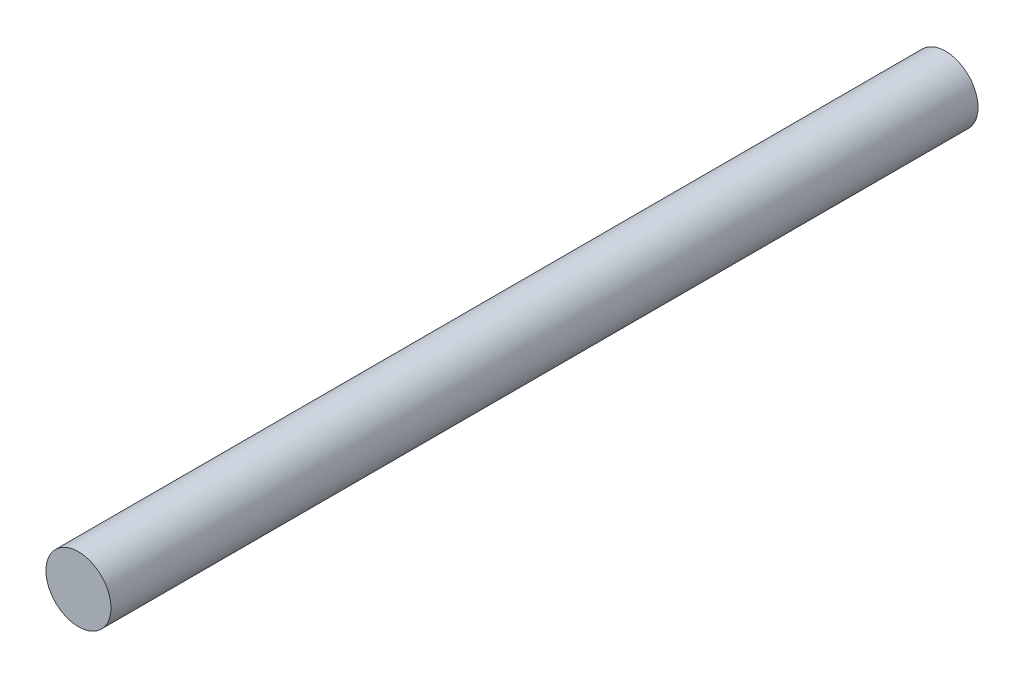
SolidWorks part; units mm, degrees
ref_plane "Front Plane" through (0, 0, 0) normal (0, 0, 1) x (1, 0, 0)
ref_plane "Top Plane" through (0, 0, 0) normal (0, 1, 0) x (1, 0, 0)
ref_plane "Right Plane" through (0, 0, 0) normal (1, 0, 0) x (0, 0, -1)
sketch "Sketch1" plane through (0, 0, 0) normal (0, 0, 1) x (1, 0, 0)
  circle A0 centre (0, 0) radius 0.75
  dimension "D1" = 1.5
extrude "Boss-Extrude1" add sketch "Sketch1" along normal blind 20
